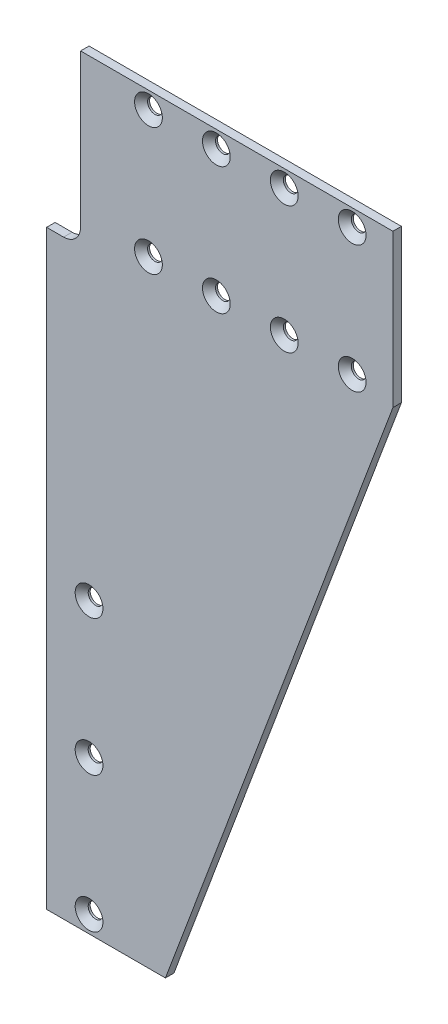
SolidWorks part; units mm, degrees
material "ASTM A36 Steel"
ref_plane "Front Plane" through (0, 0, 0) normal (0, 0, 1) x (1, 0, 0)
ref_plane "Top Plane" through (0, 0, 0) normal (0, 1, 0) x (1, 0, 0)
ref_plane "Right Plane" through (0, 0, 0) normal (1, 0, 0) x (0, 0, -1)
sketch "Sketch1" plane through (0, 0, 0) normal (0, 0, 1) x (1, 0, 0)
  line L0 (0, 0) -> (0, 220.98)
  line L7 (0, 0) -> (0, 282.9449) construction
  line L8 (6.35, 220.98) -> (0, 220.98)
  line L9 (12.7, 284.48) -> (12.7, 227.33)
  line L10 (12.7, 284.48) -> (129.54, 284.48)
  line L11 (129.54, 284.48) -> (129.54, 227.33)
  line L12 (129.54, 227.33) -> (44.45, 0)
  line L13 (44.45, 0) -> (0, 0)
  arc A1 (12.7, 227.33) -> (6.35, 220.98) centre (6.35, 227.33) cw
  point P11 (-12.7, 152.4)
  dimension "D7" = 6.35
  dimension "D1" = 220.98
  dimension "D2" = 284.48
  dimension "D3" = 44.45
  dimension "D4" = 129.54
  dimension "D5" = 12.7
  dimension "D6" = 57.15
extrude "Boss-Extrude1" add sketch "Sketch1" against normal blind 3.175
sketch "Sketch2" plane through (0, 0, 0) normal (0, 0, 1) x (1, 0, 0)
  line L0 (129.54, 284.48) -> (12.7, 284.48) construction
  line L3 (12.7, 284.48) -> (12.7, 227.33) construction
  line L8 (38.1, 278.13) -> (114.3, 278.13) construction
  line L9 (38.1, 230.505) -> (114.3, 230.505) construction
  line L10 (15.875, 57.15) -> (15.875, 6.35) construction
  line L11 (0, 0) -> (44.45, 0) construction
  line L12 (15.875, 57.15) -> (15.875, 107.95) construction
  line L13 (0, 220.98) -> (0, 0) construction
  dimension "D2" = 6.35
  dimension "D3" = 76.2
  dimension "D4" = 25.4
  dimension "D5" = 47.625
  dimension "D9" = 6.35
  dimension "D10" = 50.8
  dimension "D11" = 50.8
  dimension "D12" = 15.875
hole_wizard "CSK for #0 Flat Head Machine Screw (100)1" positions "3DSketch1" profile "Sketch3" countersink size "#0" standard "ANSI Inch" end condition through all
sketch3d "3DSketch1"
  point P12 (38.1, 278.13, 0)
  point P15 (38.1, 230.505, 0)
sketch "Sketch3" plane through (38.1, 278.13, 0) normal (1, 0, 0) x (0, -1, 0)
  line L0 (0, 0) -> (0, 3.175)
  line L1 (0, 3.175) -> (2.7559, 3.175)
  line L2 (2.7559, 3.175) -> (2.7559, 2.4384)
  line L3 (2.7559, 2.4384) -> (5.1943, 0)
  line L5 (5.1943, 0) -> (0, 0)
  line L6 (-2.7559, 2.4384) -> (-5.1943, 0) construction
  line L11 (0, -6.35) -> (0, 107.95) construction
  dimension "Thru Hole Dia." = 5.5118
  dimension "Thru Hole Depth" = 3.175
  dimension "Near C'Sink Dia." = 10.3886
  dimension "Near C'Sink Angle" = 90
pattern_linear "LPattern1" count 4 spacing 25.4 along (1, 0, 0) of "CSK for #0 Flat Head Machine Screw (100)1"
hole_wizard "CSK for #0 Flat Head Machine Screw (100)2" positions "3DSketch2" profile "Sketch4" countersink size "#0" standard "ANSI Inch" end condition through all
sketch3d "3DSketch2"
  point P6 (15.875, 107.95, 0)
sketch "Sketch4" plane through (15.875, 107.95, 0) normal (1, 0, 0) x (0, -1, 0)
  line L0 (0, 0) -> (0, 3.175)
  line L1 (0, 3.175) -> (2.7559, 3.175)
  line L2 (2.7559, 3.175) -> (2.7559, 2.4384)
  line L3 (2.7559, 2.4384) -> (5.1943, 0)
  line L5 (5.1943, 0) -> (0, 0)
  line L6 (-2.7559, 2.4384) -> (-5.1943, 0) construction
  line L11 (0, -6.35) -> (0, 107.95) construction
  dimension "Thru Hole Dia." = 5.5118
  dimension "Thru Hole Depth" = 3.175
  dimension "Near C'Sink Dia." = 10.3886
  dimension "Near C'Sink Angle" = 90
pattern_linear "LPattern2" count 3 spacing 50.8 along (0, -1, 0) of "CSK for #0 Flat Head Machine Screw (100)2"
